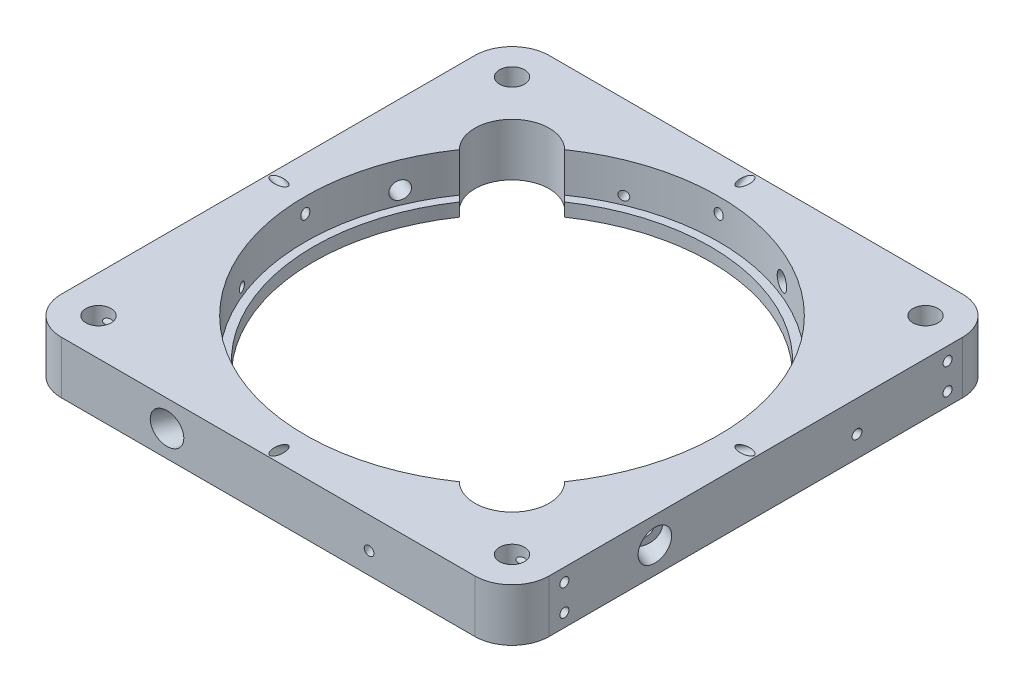
SolidWorks part; units mm, degrees
ref_plane "Front Plane" through (0, 0, 0) normal (0, 0, 1) x (1, 0, 0)
ref_plane "Top Plane" through (0, 0, 0) normal (0, 1, 0) x (1, 0, 0)
ref_plane "Right Plane" through (0, 0, 0) normal (1, 0, 0) x (0, 0, -1)
sketch "Sketch1" plane through (0, 0, 0) normal (0, 1, 0) x (1, 0, 0)
  line L1 (-50, 50) -> (50, 50) construction
  line L2 (-50, 59) -> (50, 59)
  line L3 (-59, 50) -> (-59, -50)
  line L4 (50, 50) -> (50, -50) construction
  line L5 (-50, -59) -> (50, -59)
  line L6 (50, -50) -> (-50, -50) construction
  line L7 (-50, -50) -> (-50, 50) construction
  line L8 (59, 50) -> (59, -50)
  line L9 (-59, 59) -> (59, -59) construction
  line L10 (-59, -59) -> (59, 59) construction
  circle A0 centre (50, 50) radius 3.025
  circle A1 centre (50, -50) radius 3.025
  circle A2 centre (-50, 50) radius 3.025
  circle A3 centre (-50, -50) radius 3.025
  arc A4 (-59, -50) -> (-50, -59) centre (-50, -50) ccw
  arc A5 (50, -59) -> (59, -50) centre (50, -50) ccw
  arc A6 (50, 59) -> (59, 50) centre (50, 50) cw
  arc A7 (-50, 59) -> (-59, 50) centre (-50, 50) ccw
  point P8 (50, 0)
  point P9 (0, 50)
  point P10 (0, 0)
  point P11 (-50, 0)
  point P12 (0, -50)
  dimension "D1" = 6.05
  dimension "D4" = 9
  dimension "D2" = 100
  dimension "D3" = 9
extrude "Boss-Extrude1" add sketch "Sketch1" along normal blind 12.7
sketch "Sketch2" plane through (59, 0, 0) normal (1, 0, 0) x (0, 0, -1)
  line L0 (46.34, 12.7) -> (46.975, 12.7) construction
  line L1 (46.34, 12.7) -> (46.34, 9.525) construction
  line L2 (-50, 12.7) -> (50, 12.7) construction
  line L3 (46.34, 9.525) -> (46.34, 3.175) construction
  line L4 (46.34, 3.175) -> (46.34, 0) construction
  line L5 (-50, 0) -> (50, 0) construction
  line L6 (-46.34, 12.7) -> (-46.34, 9.525) construction
  line L7 (-46.34, 9.525) -> (-46.34, 3.175) construction
  line L8 (-46.34, 3.175) -> (-46.34, 0) construction
  line L9 (-46.975, 12.7) -> (-46.34, 12.7) construction
  circle A0 centre (-46.34, 9.525) radius 1.095
  circle A1 centre (-46.34, 3.175) radius 1.095
  circle A2 centre (46.34, 9.525) radius 1.095
  circle A3 centre (46.34, 3.175) radius 1.095
  dimension "D1" = 2.19
  dimension "D2" = 3.175
  dimension "D3" = 0.635
extrude "Cut-Extrude1" cut sketch "Sketch2" against normal blind 15
mirror "Mirror1" about plane through (0, 0, 0) normal (1, 0, 0) of "Cut-Extrude1"
sketch "Sketch4" plane through (0, 0, 0) normal (0, 0, 1) x (1, 0, 0)
  line L0 (0, 0) -> (0, 12.7)
  line L1 (-50, 12.7) -> (50, 12.7) construction
  line L2 (0, 12.7) -> (50, 12.7)
  line L3 (50, 12.7) -> (50, 3.175)
  line L4 (50, 3.175) -> (48, 3.175)
  line L5 (48, 3.175) -> (48, 0)
  line L6 (-50, 0) -> (50, 0) construction
  line L7 (48, 0) -> (0, 0)
  dimension "D1" = 2
  dimension "D2" = 50
  dimension "D3" = 9.525
revolve "Cut-Revolve1" cut sketch "Sketch4" angle 360 about L0
ref_axis "Axis1" through (0, 13.335, 0) along (0, -1, 0)
ref_plane "Plane1" through (0, 0, 0) normal (-0.3827, 0, 0.9239) x (0.9239, 0, 0.3827)
sketch "Sketch5" plane through (0, 0, 0) normal (-0.3827, 0, 0.9239) x (0.9239, 0, 0.3827)
  line L0 (0, 12.7) -> (0, 0) construction
  line L1 (0, 13.335) -> (0, -0.635) construction
  line L2 (-23.6157, 12.7) -> (68.7723, 12.7) construction
  line L5 (-23.6157, 0) -> (68.7723, 0) construction
  circle A0 centre (0, 6.35) radius 2.1
  point P10 (0, 6.35)
  dimension "D2" = 4.2
extrude "Cut-Extrude2" cut sketch "Sketch5" against normal through all
ref_plane "Plane2" through (0, 0, 0) normal (-0.9239, 0, 0.3827) x (0.3827, 0, 0.9239)
sketch "Sketch6" plane through (0, 0, 0) normal (-0.9239, 0, 0.3827) x (0.3827, 0, 0.9239)
  line L1 (0, 12.7) -> (0, 3.175) construction
  line L2 (-68.7723, 12.7) -> (23.6157, 12.7) construction
  line L3 (50, 12.7) -> (-50, 12.7) construction
  line L4 (50, 3.175) -> (-50, 3.175) construction
  line L5 (0, 13.335) -> (0, -0.635) construction
  circle A0 centre (0, 5.175) radius 1.095
  dimension "D1" = 2.19
  dimension "D2" = 2
extrude "Cut-Extrude3" cut sketch "Sketch6" against normal through all
ref_plane "Plane3" through (0, 0, 50) normal (0, 0, -1) x (-1, 0, 0)
ref_plane "Plane4" through (0, 25.5477, 44.25) normal (0, -0.5, -0.866) x (-1, 0, 0)
sketch "Sketch7" plane through (0, 25.5477, 44.25) normal (0, -0.5, -0.866) x (-1, 0, 0)
  line L0 (0, -14.0015) -> (0, -17.1765) construction
  line L1 (0, 11.5484) -> (0, -0.5499) construction
  circle A0 centre (0, -17.1765) radius 1.095
  ellipse E1 centre (0, 10.9985) end of major axis (-50, 10.9985) minor radius 25 construction
  dimension "D1" = 2.19
  dimension "D2" = 3.175
extrude "Cut-Extrude4" cut sketch "Sketch7" against normal up to surface and the other way up to surface up to face at (50, 12.7, 0) other way up to face at (45.7757, 5.4266, -20.1144)
pattern_circular "CirPattern1" count 4 over 360 about axis through (0, 13.335, 0) along (0, -1, 0) of "Cut-Extrude2", "Cut-Extrude3", "Cut-Extrude4"
sketch "Sketch8" plane through (0, 12.7, 0) normal (0, 1, 0) x (1, 0, 0)
  line L0 (-41.1418, 28.4139) -> (-39.7031, 26.9752)
  line L1 (-39.7031, 26.9752) -> (-26.9752, 39.7031)
  line L2 (-26.9752, 39.7031) -> (-28.4139, 41.1418)
  line L3 (0, 0) -> (-34.7779, 34.7779) construction
  line L4 (-34.7779, 34.7779) -> (-56.364, 56.364) construction
  arc A0 (-41.1418, 28.4139) -> (-28.4139, 41.1418) centre (-34.7779, 34.7779) cw
  circle A1 centre (0, 0) radius 50 construction
  circle A2 centre (0, 0) radius 48 construction
  arc A4 (-50, 59) -> (-59, 50) centre (-50, 50) ccw construction
  point P3 (-33.3392, 33.3392)
  dimension "D2" = 9
  dimension "D1" = 18
extrude "Cut-Extrude5" cut sketch "Sketch8" against normal through all
pattern_circular "CirPattern2" count 2 over 360 about axis through (0, 0, 0) along (0, 1, 0) of "Cut-Extrude5"
sketch "Sketch9" plane through (0, 0, 0) normal (-0.3827, 0, 0.9239) x (0.9239, 0, 0.3827)
  line L0 (0, 13.335) -> (0, -0.635) construction
  circle A0 centre (0, 6.35) radius 3.75
  circle A1 centre (0, 6.35) radius 2.1 construction
  dimension "D1" = 7.5
extrude "Cut-Extrude6" cut sketch "Sketch9" along normal blind 5 and the other way through all from offset 63.3333
pattern_circular "CirPattern6" count 4 over 360 about axis through (0, 0, 0) along (0, 1, 0) of "Cut-Extrude6"
